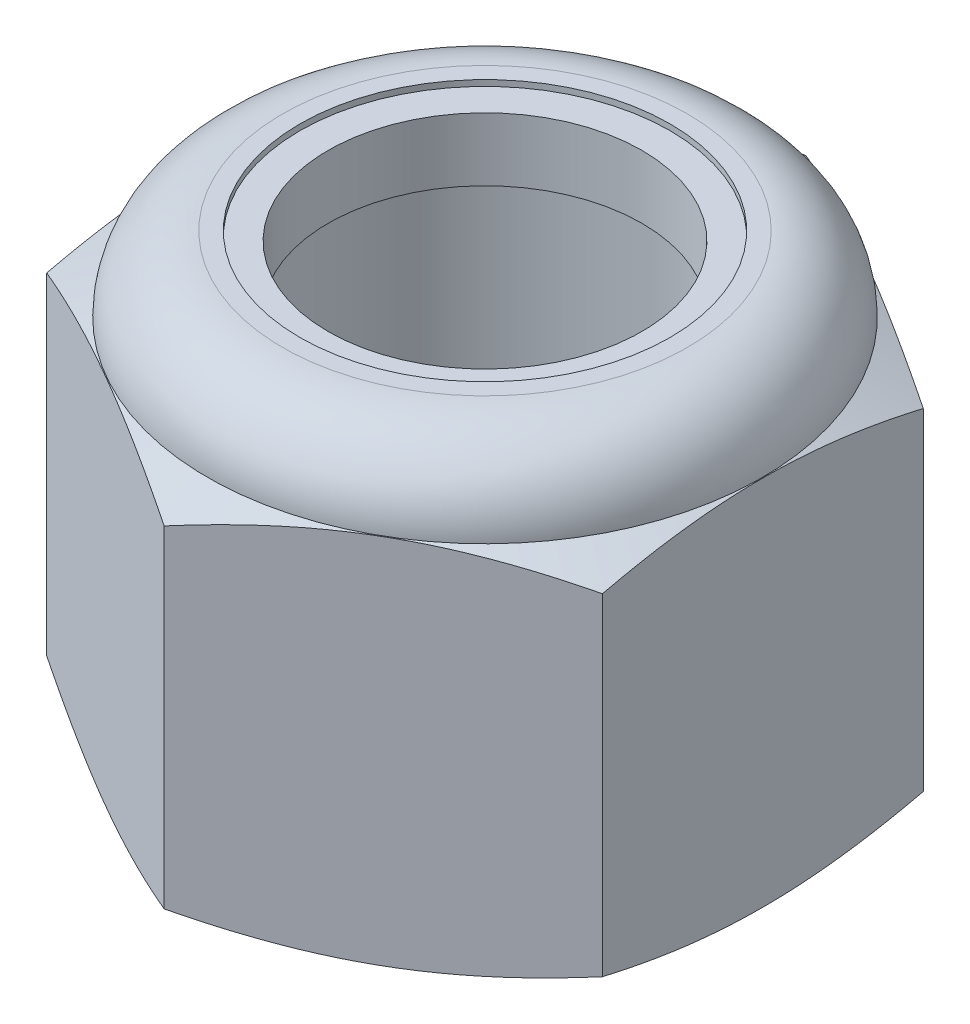
SolidWorks part; units mm, degrees
ref_plane "Front Plane" through (0, 0, 0) normal (0, 0, 1) x (1, 0, 0)
ref_plane "Top Plane" through (0, 0, 0) normal (0, 1, 0) x (1, 0, 0)
ref_plane "Right Plane" through (0, 0, 0) normal (1, 0, 0) x (0, 0, -1)
sketch "Sketch1" plane through (0, 0, 0) normal (0, 1, 0) x (1, 0, 0)
  line L0 (0, 0) -> (0, 8.2562) construction
  line L2 (0, 8.2562) -> (-7.1501, 4.1281)
  line L3 (-7.1501, 4.1281) -> (-7.1501, -4.1281)
  line L4 (-7.1501, -4.1281) -> (0, -8.2562)
  line L5 (0, -8.2562) -> (7.1501, -4.1281)
  line L6 (7.1501, -4.1281) -> (7.1501, 4.1281)
  line L7 (7.1501, 4.1281) -> (0, 8.2562)
  circle A0 centre (0, 0) radius 7.1501 construction
  dimension "D1" = 14.3002
extrude "Boss-Extrude1" add sketch "Sketch1" along normal blind 11.5094
sketch "Sketch2" plane through (0, 11.5094, 0) normal (0, 1, 0) x (1, 0, 0)
  circle A0 centre (0, 0) radius 4.7625
  dimension "D1" = 9.525
extrude "Cut-Extrude1" cut sketch "Sketch2" against normal through all
sketch "Sketch4" plane through (0, 0, 0) normal (1, 0, 0) x (0, 0, -1)
  line L0 (0, 0) -> (7.1386, 0)
  line L2 (8.2562, 11.5094) -> (8.2562, 0) construction
  line L3 (8.2562, 0.5211) -> (8.2562, 9.0578)
  line L4 (8.2562, 9.0578) -> (7.1386, 9.579)
  line L5 (4.1281, 11.5094) -> (8.2562, 11.5094) construction
  line L6 (5.2082, 11.5094) -> (5.2082, 12.7794)
  line L7 (5.2082, 12.7794) -> (9.5262, 12.7794)
  line L8 (9.5262, 12.7794) -> (9.5262, -1.27)
  line L9 (9.5262, -1.27) -> (0, -1.27)
  line L10 (0, -1.27) -> (0, 0)
  line L11 (-4.1281, 0) -> (4.1281, 0) construction
  line L12 (4.1281, 0) -> (8.2562, 0) construction
  line L13 (7.1386, 0) -> (8.2562, 0.5211)
  line L14 (7.1386, 0) -> (7.1386, 9.579) construction
  line L15 (0, 0) -> (0, 9.6306) construction
  arc A0 (7.1386, 9.579) -> (5.2082, 11.5094) centre (5.2082, 9.579) ccw
  dimension "D1" = 1.27
  dimension "D2" = 25
  dimension "D3" = 1.9304
  dimension "D4" = 1.1176
  dimension "D5" = 1.27
revolve "Cut-Revolve1" cut sketch "Sketch4" angle 360 about L15
sketch "Sketch5" plane through (0, 0, 0) normal (1, 0, 0) x (0, 0, -1)
  line L0 (6.9862, 9.579) -> (0, 9.579)
  line L1 (7.1386, 9.579) -> (-7.1386, 9.579) construction
  line L2 (0, 9.579) -> (0, 12.119)
  line L3 (0, 12.119) -> (4.6228, 12.119)
  line L4 (4.6228, 12.119) -> (4.6228, 11.357)
  line L5 (4.6228, 11.357) -> (5.2082, 11.357)
  line L6 (5.2082, 11.357) -> (5.2082, 11.5094) construction
  line L7 (5.2082, 11.5094) -> (-5.2082, 11.5094) construction
  arc A0 (5.2082, 11.357) -> (6.9862, 9.579) centre (5.2082, 9.579) cw
  arc A1 (7.1386, 9.579) -> (5.2082, 11.5094) centre (5.2082, 9.579) ccw construction
  dimension "D1" = 0.1524
  dimension "D2" = 4.6228
  dimension "D3" = 2.54
revolve "Cut-Revolve2" cut sketch "Sketch5" angle 360 about L2
sketch "Sketch6" plane through (0, 0, 0) normal (1, 0, 0) x (0, 0, -1)
  line L1 (4.0386, 9.6552) -> (4.0386, 11.2808)
  line L2 (4.0386, 11.2808) -> (5.2082, 11.2808)
  line L3 (4.7625, 11.5094) -> (-4.7625, 11.5094) construction
  line L5 (-5.2082, 11.357) -> (5.2082, 11.357) construction
  line L6 (6.9083, 9.6552) -> (4.0386, 9.6552)
  line L7 (7.1386, 9.579) -> (-7.1386, 9.579) construction
  line L8 (0, 0) -> (0, 11.5094) construction
  arc A0 (6.9083, 9.6552) -> (5.2082, 11.2808) centre (5.2082, 9.579) ccw
  arc A4 (6.9862, 9.579) -> (5.2082, 11.357) centre (5.2082, 9.579) ccw construction
  dimension "D1" = 0.0762
  dimension "D2" = 0.0762
  dimension "D3" = 4.0386
revolve "Revolve1" add sketch "Sketch6" angle 360 about L8
